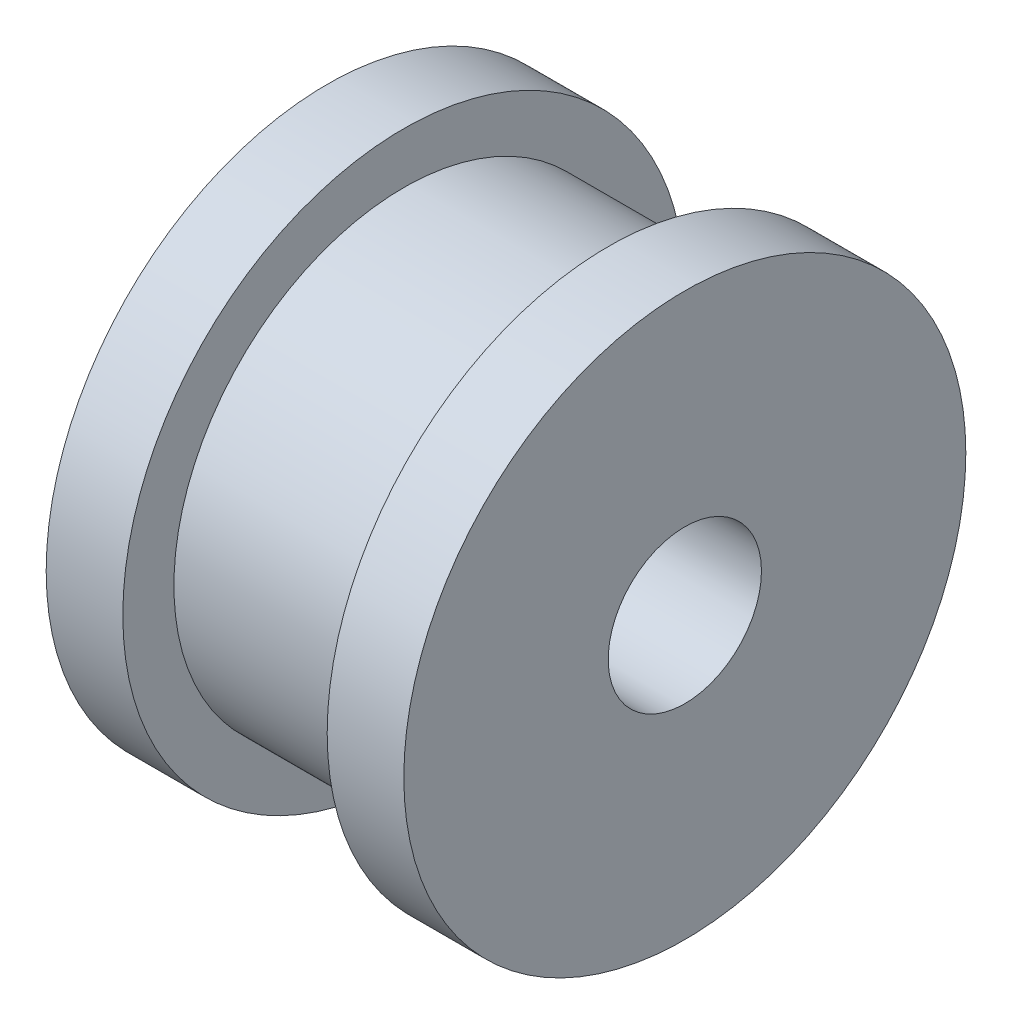
SolidWorks part; units mm, degrees
ref_plane "Piano frontale" through (0, 0, 0) normal (0, 0, 1) x (1, 0, 0)
ref_plane "Piano superiore" through (0, 0, 0) normal (0, 1, 0) x (1, 0, 0)
ref_plane "Piano destro" through (0, 0, 0) normal (1, 0, 0) x (0, 0, -1)
sketch "Sketch1" plane through (0, 0, 0) normal (1, 0, 0) x (0, 0, -1)
  circle A0 centre (0, 0) radius 9
  dimension "D1" = 18
extrude "Boss-Extrude1" add sketch "Sketch1" along normal blind 8
sketch "Sketch2" plane through (8, 0, 0) normal (1, 0, 0) x (0, 0, -1)
  circle A4 centre (0, 0) radius 3
  point P14 (-1.5, 4.7697)
  dimension "D1" = 6
sketch "Sketch3" plane through (8, 0, 0) normal (1, 0, 0) x (0, 0, -1)
  circle A0 centre (0, 0) radius 11
  dimension "D1" = 22
extrude "Boss-Extrude2" add sketch "Sketch3" along normal blind 3
sketch "Sketch4" plane through (0, 0, 0) normal (-1, 0, 0) x (0, 0, 1)
  circle A0 centre (0, 0) radius 11
  dimension "D1" = 22
extrude "Boss-Extrude3" add sketch "Sketch4" along normal blind 3
extrude "Cut-Extrude1" cut sketch "Sketch2" against normal blind 11 and the other way blind 3
